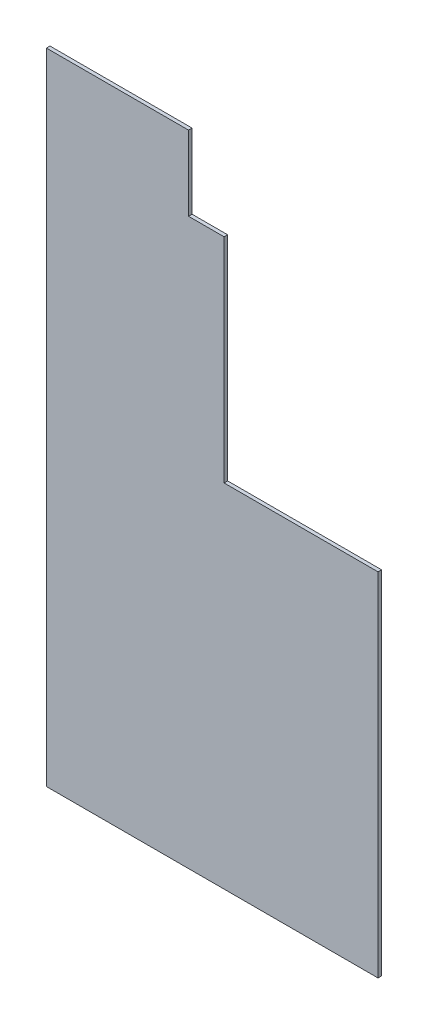
SolidWorks part; units mm, degrees
ref_plane "Plan de face" through (0, 0, 0) normal (0, 0, 1) x (1, 0, 0)
ref_plane "Plan de dessus" through (0, 0, 0) normal (0, 1, 0) x (1, 0, 0)
ref_plane "Plan de droite" through (0, 0, 0) normal (1, 0, 0) x (0, 0, -1)
sketch "Esquisse1" plane through (0, 0, 0) normal (0, 0, 1) x (1, 0, 0)
  line L0 (228.4611, -156.1865) -> (228.4611, -453.1865)
  line L1 (-51.5389, 86.8135) -> (68.4611, 86.8135)
  line L2 (-51.5389, 86.8135) -> (-51.5389, -453.1865)
  line L3 (-51.5389, -453.1865) -> (228.4611, -453.1865)
  line L4 (98.4611, -156.1865) -> (228.4611, -156.1865)
  line L6 (98.4611, 23.8135) -> (98.4611, -156.1865)
  line L9 (98.4611, 23.8135) -> (68.4611, 23.8135)
  line L10 (68.4611, 86.8135) -> (68.4611, 23.8135)
  dimension "D2" = 280
  dimension "D3" = 540
  dimension "D1" = 150
  dimension "D5" = 243
  dimension "D4" = 30
  dimension "D6" = 63
extrude "Boss.-Extru.1" add sketch "Esquisse1" along normal blind 3
equation "\"EpaisseurPlaque\"= 3"
equation "\"D1@Boss.-Extru.1\"=\"EpaisseurPlaque\""
equation "\"ProfondeurBoite\"=460"
equation "\"LongueurSyphon\"=270"
equation "\"LargeurSyphon\"=120"
equation "\"HauteurCoteDroit\"= 490"
equation "\"HauteurCoteGauche\"= 540"
equation "\"HauteurSolSyphon\"= 300"
equation "\"HauteurSyphon\"=\"HauteurCoteGauche\"-\"HauteurSolSyphon\""
equation "\"LargeurBoite\"= \"LargeurDroite\" + \"LargeurGauche\" + \"LargeurSyphon\""
equation "\"D3@Esquisse1\"=\"HauteurCoteGauche\""
equation "\"D2@Esquisse1\"=\"LargeurBoite\""
equation "\"LargeurDroite\"=10"
equation "\"LargeurGauche\"=150"
equation "\"D1@Esquisse1\"=\"LargeurGauche\""
equation "\"D5@Esquisse1\"=\"HauteurSyphon\" +\"EpaisseurPlaque\""
